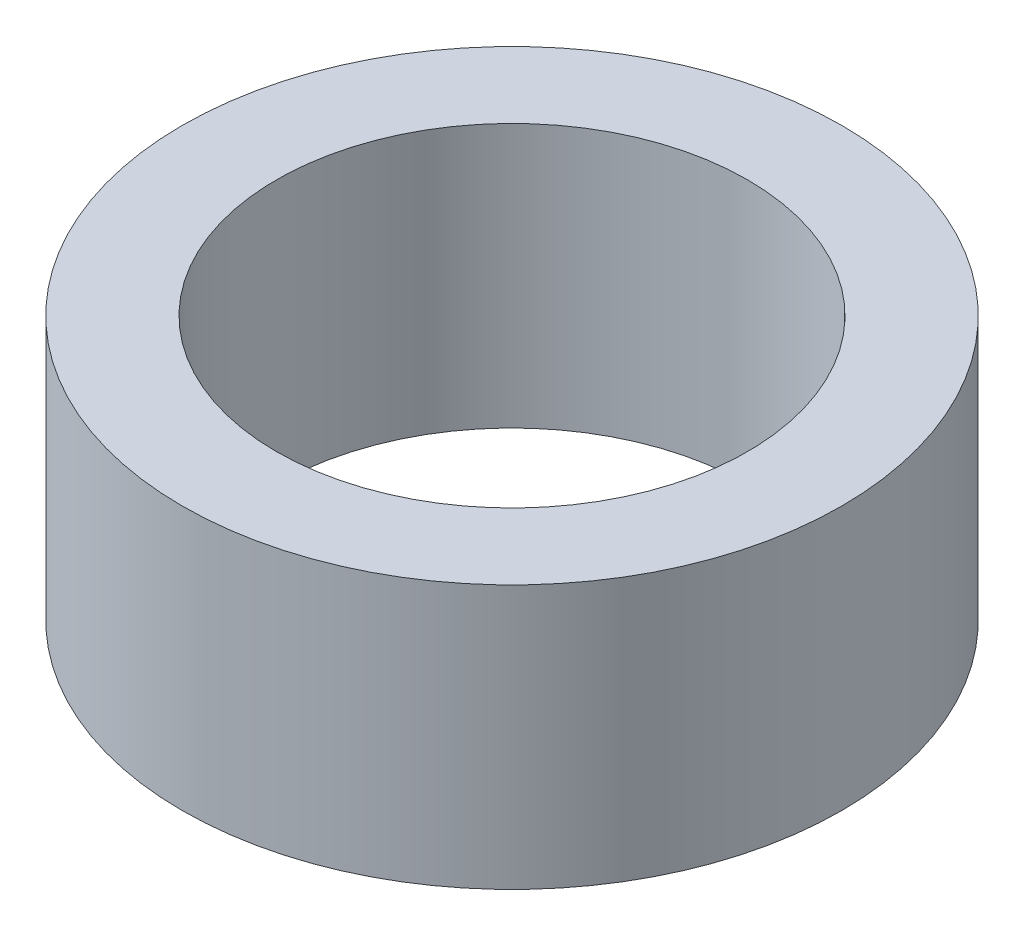
SolidWorks part; units mm, degrees
material "6061-T6 (SS)"
ref_plane "X-Y Datum" through (0, 0, 0) normal (0, 0, 1) x (1, 0, 0)
ref_plane "X-Z Datum" through (0, 0, 0) normal (0, 1, 0) x (1, 0, 0)
ref_plane "Y-Z Datum" through (0, 0, 0) normal (1, 0, 0) x (0, 0, -1)
sketch "Sketch1" plane through (0, 0, 0) normal (0, 1, 0) x (1, 0, 0)
  circle A0 centre (0, 0) radius 3.9688
  circle A1 centre (0, 0) radius 5.5562
  dimension "D1" = 7.9375
  dimension "D2" = 11.1125
  dimension "D3" = 1.5875
extrude "Boss-Extrude1" add sketch "Sketch1" against normal blind 4.445
